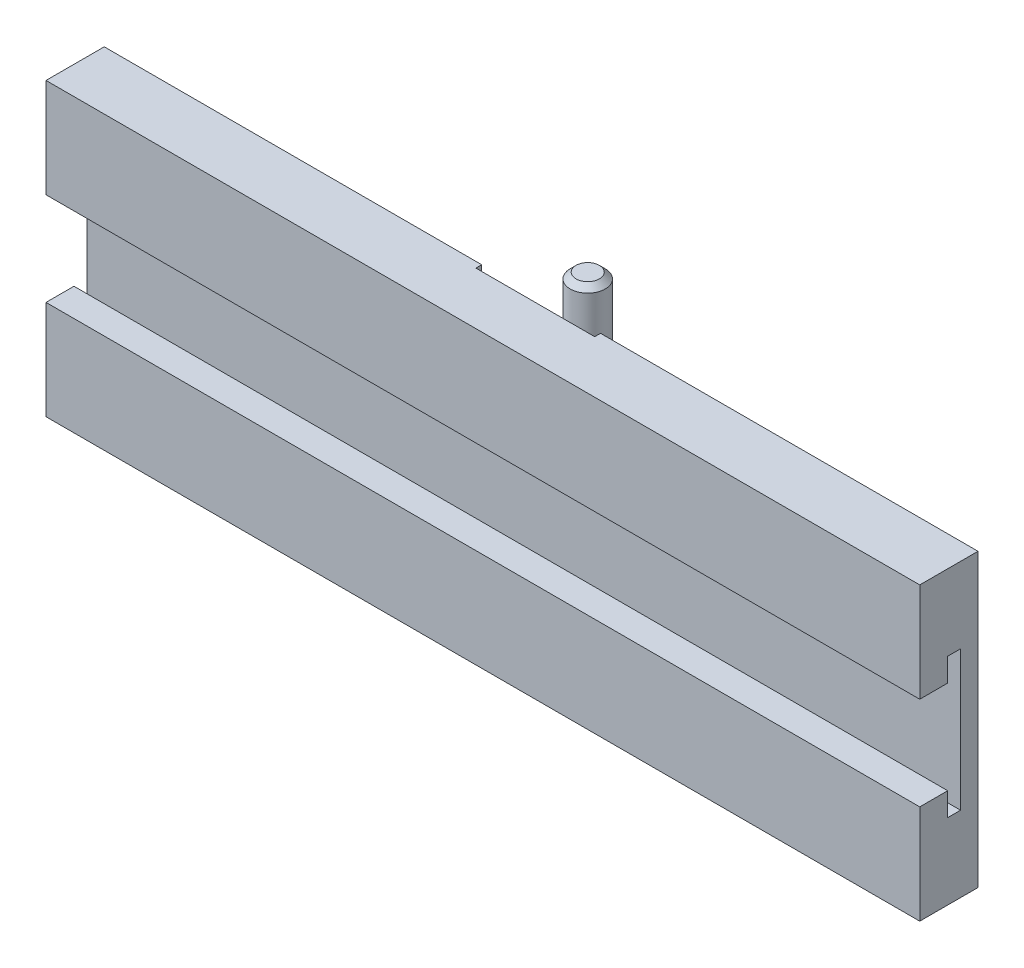
SolidWorks part; units mm, degrees
ref_plane "前视基准面" through (0, 0, 0) normal (0, 0, 1) x (1, 0, 0)
ref_plane "上视基准面" through (0, 0, 0) normal (0, 1, 0) x (1, 0, 0)
ref_plane "右视基准面" through (0, 0, 0) normal (1, 0, 0) x (0, 0, -1)
sketch "草图1" plane through (0, 0, 0) normal (0, 0, 1) x (1, 0, 0)
  line L1 (-24.7306, 0) -> (125.2694, 0)
  line L2 (-24.7306, 0) -> (-24.7306, 50)
  line L3 (-24.7306, 50) -> (125.2694, 50)
  line L4 (125.2694, 0) -> (125.2694, 50)
extrude "凸台-拉伸1" add sketch "草图1" along normal blind 10 contours L2 L3 L4 L1
sketch "草图2" plane through (125.2694, 0, 0) normal (1, 0, 0) x (0, 0, -1)
  line L0 (-10, 25) -> (17.6481, 25) construction
  line L1 (-10, 0) -> (-10, 50) construction
  line L2 (0, 25) -> (-3, 25) construction
  line L3 (0, 0) -> (0, 50) construction
  line L4 (-3, 13) -> (-3, 37)
  line L5 (-3, 37) -> (-5.2, 37)
  line L6 (-5.2, 37) -> (-5.2, 33)
  line L7 (-5.2, 33) -> (-10, 33)
  line L8 (-10, 33) -> (-10, 17)
  line L9 (-5.2, 17) -> (-10, 17)
  line L10 (-5.2, 13) -> (-5.2, 17)
  line L11 (-3, 13) -> (-5.2, 13)
extrude "切除-拉伸1" cut sketch "草图2" against normal blind 150
sketch "草图3" plane through (0, 50, 0) normal (0, 1, 0) x (1, 0, 0)
  line L0 (-24.7306, 0) -> (125.2694, 0) construction
  line L1 (-24.7306, 0) -> (125.2694, 0) construction
  line L2 (50.2694, 0) -> (50.2694, -1) construction
  line L3 (60.4694, 0) -> (40.0694, 0)
  line L4 (40.0694, 0) -> (40.0694, -1)
  line L5 (40.0694, -1) -> (60.4694, -1)
  line L6 (60.4694, 0) -> (60.4694, -1)
extrude "切除-拉伸2" cut sketch "草图3" against normal blind 150
sketch "草图4" plane through (0, 0, 1) normal (0, 0, -1) x (-1, 0, 0)
  line L0 (-60.4694, 0) -> (-60.4694, 50) construction
  line L1 (-40.0694, 0) -> (-60.4694, 0)
  line L2 (-40.0694, 0) -> (-40.0694, 5)
  line L3 (-40.0694, 5) -> (-60.4694, 5)
  line L4 (-60.4694, 0) -> (-60.4694, 5)
extrude "凸台-拉伸2" add sketch "草图4" along normal blind 12
sketch "草图5" plane through (0, 5, 0) normal (0, 1, 0) x (1, 0, 0)
  line L0 (50.2694, 11) -> (50.2694, 8) construction
  line L1 (40.0694, 11) -> (60.4694, 11) construction
  circle A0 centre (50.2694, 8) radius 3.01
extrude "凸台-拉伸3" add sketch "草图5" along normal blind 45
chamfer "倒角2" distance 1 angle 45 1 edges at (47.2594, 50, -8)
